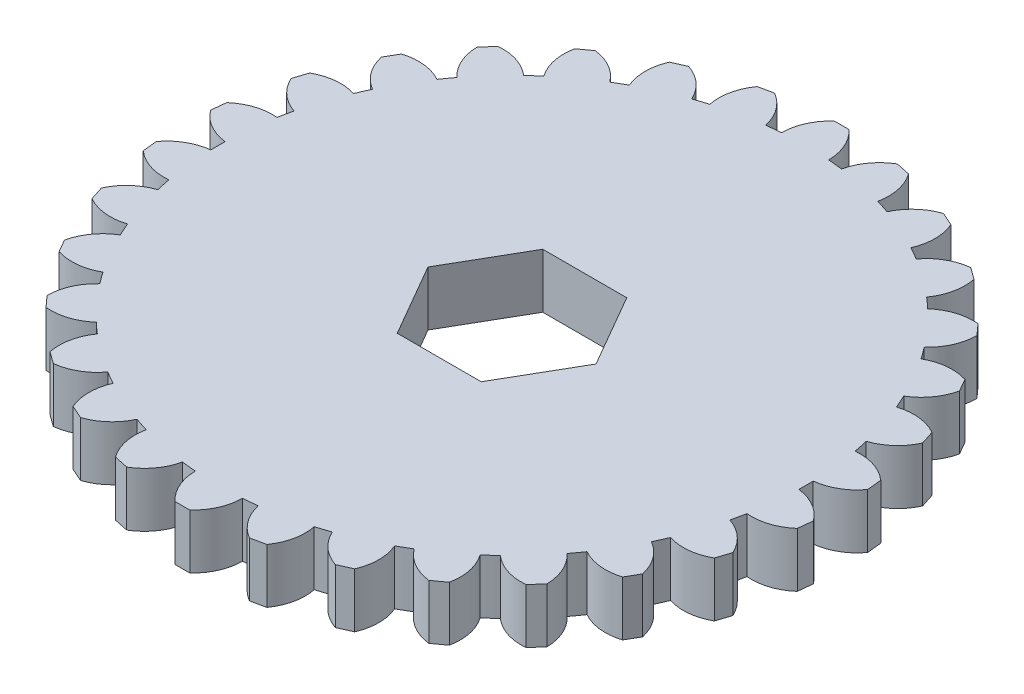
SolidWorks part; units mm, degrees
ref_plane "Front Plane" through (0, 0, 0) normal (0, 0, 1) x (1, 0, 0)
ref_plane "Top Plane" through (0, 0, 0) normal (0, 1, 0) x (1, 0, 0)
ref_plane "Right Plane" through (0, 0, 0) normal (1, 0, 0) x (0, 0, -1)
sketch "Sketch2" plane through (0, 0, 0) normal (0, 1, 0) x (1, 0, 0)
  line L1 (7.3323, 0) -> (3.6662, 6.35)
  line L2 (3.6662, 6.35) -> (-3.6662, 6.35)
  line L3 (-3.6662, 6.35) -> (-7.3323, 0)
  line L4 (-7.3323, 0) -> (-3.6662, -6.35)
  line L5 (-3.6662, -6.35) -> (3.6662, -6.35)
  line L6 (3.6662, -6.35) -> (7.3323, 0)
  circle A0 centre (0, 0) radius 25.6642
  circle A1 centre (0, 0) radius 6.35 construction
  dimension "D1" = 51.3283
  dimension "D2" = 12.7
  dimension "D3" = 6.35
extrude "Boss-Extrude2" add sketch "Sketch2" along normal blind 4.7625
sketch "Sketch1" plane through (0, 0, 0) normal (0, 1, 0) x (1, 0, 0)
  line L0 (0, 0) -> (-3.0233, 28.765) construction
  line L1 (0, 0) -> (3.0233, 28.765) construction
  line L2 (3.0233, 28.765) -> (-3.0233, 28.765) construction
  line L3 (-0.6402, 28.765) -> (0.6402, 28.765)
  line L4 (1.7263, 27.2139) -> (2.0551, 25.3491) construction
  line L5 (-1.7263, 27.2139) -> (-2.0551, 25.3491) construction
  line L6 (-1.7263, 27.2139) -> (-0.6402, 28.765) construction
  line L7 (1.7263, 27.2139) -> (0.6402, 28.765) construction
  line L8 (0, 28.765) -> (0, 0) construction
  arc A1 (-2.7445, 25.2837) -> (2.0551, 25.3491) centre (0, 0) cw
  arc A2 (-0.6402, 28.765) -> (-2.0551, 25.3491) centre (2.315, 25.5399) ccw
  arc A3 (0.6402, 28.765) -> (2.0551, 25.3491) centre (-2.315, 25.5399) cw
  circle A4 centre (0, 0) radius 25.4322 construction
  circle A5 centre (0, 0) radius 27.2686 construction
  point P18 (-1.7263, 27.2139)
  dimension "D1" = 54.5371
  dimension "D8" = 3.4924
  dimension "D9" = 50.8645
  dimension "D2" = 12
  dimension "D6" = 10
  dimension "D7" = 35
  dimension "D3" = 4.8072
  dimension "D4" = 2.55
  dimension "D5" = 1.56
extrude "Boss-Extrude3" add sketch "Sketch1" along normal blind 4.7625
pattern_circular "CirPattern1" count 30 over 360 about axis through (0, 0, 0) along (0, 1, 0) of "Boss-Extrude3"
